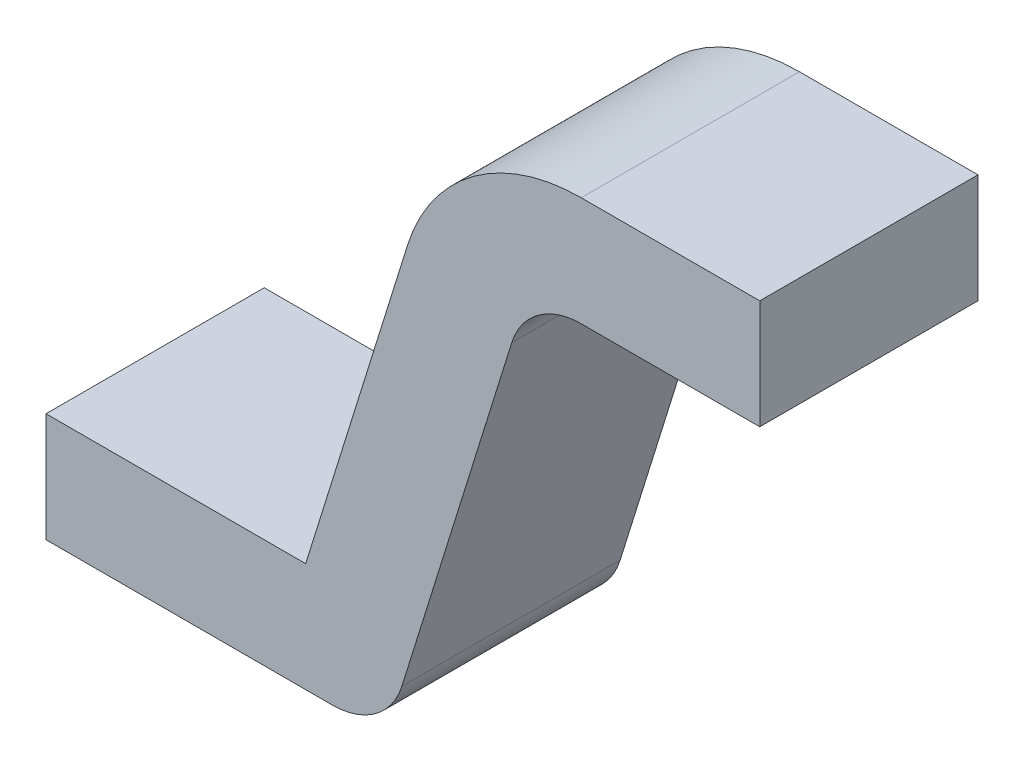
SolidWorks part; units mm, degrees
ref_plane "Plan de face" through (0, 0, 0) normal (0, 0, 1) x (1, 0, 0)
ref_plane "Plan de dessus" through (0, 0, 0) normal (0, 1, 0) x (1, 0, 0)
ref_plane "Plan de droite" through (0, 0, 0) normal (1, 0, 0) x (0, 0, -1)
sketch "Esquisse1" plane through (0, 0, 0) normal (0, 0, 1) x (1, 0, 0)
  line L0 (0, 0) -> (0.3937, 0)
  line L1 (0, 0) -> (0, 0.489) construction
  line L2 (0, 0) -> (0.5, 0) construction
  line L3 (0, 0.7) -> (1.0574, 0.7) construction
  line L4 (0, 0.7) -> (0.5, 0.7) construction
  line L5 (0.7357, 0.625) -> (0.9812, 0.625)
  line L6 (0, 0.15) -> (0.357, 0.15)
  line L7 (0.4892, 0.0702) -> (0.6403, 0.5548)
  line L8 (0.357, 0.15) -> (0.497, 0.5994)
  line L9 (0.7357, 0.775) -> (0.9812, 0.775)
  line L10 (0, 0.625) -> (1.0574, 0.625) construction
  line L11 (0.9812, 0.775) -> (0.9812, 0.625)
  line L12 (0, 0.15) -> (0, 0)
  arc A0 (0.7357, 0.625) -> (0.6403, 0.5548) centre (0.7357, 0.525) ccw
  arc A1 (0.4892, 0.0702) -> (0.3937, 0) centre (0.3937, 0.1) cw
  arc A2 (0.357, 0.15) -> (0.357, 0.15) centre (0.357, 0.15) cw
  arc A3 (0.7357, 0.775) -> (0.497, 0.5994) centre (0.7357, 0.525) ccw
  dimension "D1" = 0.1
  dimension "D2" = 0.7
  dimension "D3" = 0.075
  dimension "D4" = 0.15
extrude "Boss.-Extru.1" add sketch "Esquisse1" along normal blind 0.3
